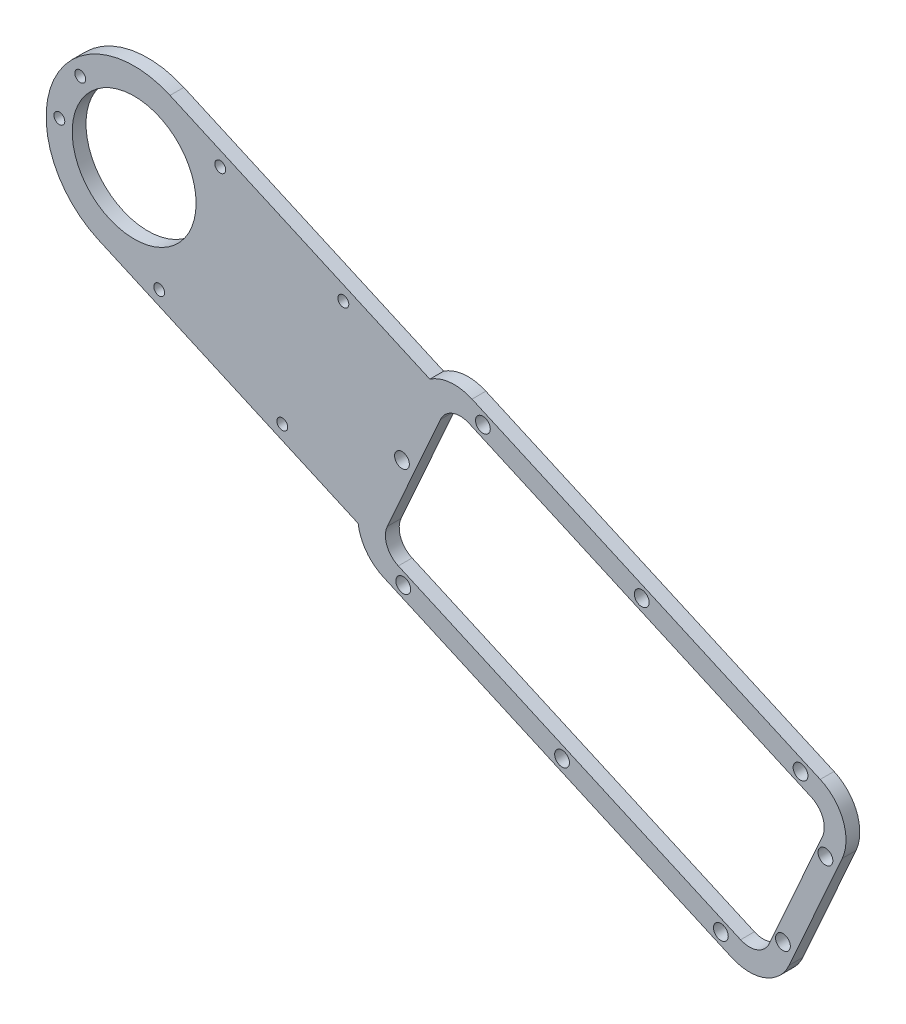
SolidWorks part; units mm, degrees
ref_plane "Front Plane" through (0, 0, 0) normal (0, 0, 1) x (1, 0, 0)
ref_plane "Top Plane" through (0, 0, 0) normal (0, 1, 0) x (1, 0, 0)
ref_plane "Right Plane" through (0, 0, 0) normal (1, 0, 0) x (0, 0, -1)
sketch "Sketch1" plane through (0, 0, 0) normal (0, 0, 1) x (1, 0, 0)
  line L0 (-81.4496, 53.8056) -> (-67.7738, 84.4844) construction
  line L1 (-91.6421, 47.2686) -> (-171.5223, 82.8771) construction
  line L2 (-75.2645, 89.2365) -> (-149.4221, 122.2941) construction
  line L3 (-72.7153, 90.8373) -> (-152.817, 126.5446)
  line L5 (-173.1746, 80.8766) -> (-93.0729, 45.1693)
  line L6 (-79.8678, 50.2314) -> (-67.6532, 77.6322)
  line L7 (-176.5357, 89.3012) -> (-161.0339, 124.0762) construction
  line L8 (-168.9326, 106.3571) -> (-73.7605, 63.9318) construction
  line L9 (-133.1238, 63.0229) -> (-112.7662, 108.691) construction
  line L10 (-162.5246, 125.6714) -> (-222.2994, 152.3174)
  line L11 (-73.7605, 63.9318) -> (-275.2251, 153.7395) construction
  line L12 (-179.0143, 88.6803) -> (-238.789, 115.3263)
  circle A0 centre (-230.5442, 133.8219) radius 14.25
  circle A2 centre (-95.5715, 49.0202) radius 1.7
  arc A3 (-152.817, 126.5446) -> (-162.5246, 125.6714) centre (-156.8885, 117.411) ccw
  arc A4 (-179.0143, 88.6803) -> (-173.1746, 80.8766) centre (-169.1031, 90.0102) ccw
  arc A5 (-93.0729, 45.1693) -> (-79.8678, 50.2314) centre (-89.0014, 54.3029) ccw
  arc A6 (-67.6532, 77.6322) -> (-72.7153, 90.8373) centre (-76.7868, 81.7037) ccw
  circle A7 centre (-132.1059, 65.3063) radius 1.7
  circle A8 centre (-168.6403, 81.5924) radius 1.7
  circle A9 centre (-150.3184, 122.6936) radius 1.7
  circle A10 centre (-113.784, 106.4076) radius 1.7
  circle A11 centre (-77.2496, 90.1215) radius 1.7
  circle A13 centre (-81.2951, 54.1522) radius 1.7
  circle A14 centre (-71.5234, 76.0729) radius 1.7
  circle A17 centre (-168.9326, 106.3571) radius 1.7
  arc A18 (-222.2994, 152.3174) -> (-238.789, 115.3263) centre (-230.5442, 133.8219) ccw
  dimension "D4" = 12
  dimension "D6" = 3.4
  dimension "D7" = 3.4
  dimension "D8" = 3.4
  dimension "D9" = 3.4
  dimension "D10" = 3.4
  dimension "D11" = 3.4
  dimension "D12" = 3.4
  dimension "D14" = 3.4
  dimension "D23" = 28.5
  dimension "D25" = 6
  dimension "D3" = 12
  dimension "D5" = 171.6559
  dimension "D1" = 2.5
  dimension "D2" = 2.5
  dimension "D15" = 0
  dimension "D16" = 0
  dimension "D17" = 40
  dimension "D18" = 40
  dimension "D20" = 40
  dimension "D21" = 40
extrude "Boss-Extrude1" add sketch "Sketch1" along normal blind 3.175
sketch "Sketch5" plane through (0, 0, 3.175) normal (0, 0, 1) x (1, 0, 0)
  line L0 (-181.3663, 93.0133) -> (-237.5676, 118.0664) construction
  line L1 (-238.789, 115.3263) -> (-179.0143, 88.6803) construction
  line L2 (-165.0202, 123.4993) -> (-223.5208, 149.5773) construction
  line L3 (-162.5246, 125.6714) -> (-222.2994, 152.3174) construction
  line L4 (-168.9326, 106.3571) -> (-249.0397, 142.0667) construction
  line L5 (-230.5442, 133.8219) -> (-247.7516, 135.033) construction
  line L6 (-242.9474, 145.8104) -> (-230.5442, 133.8219) construction
  line L7 (-196.4664, 99.7446) -> (-182.4196, 131.2555) construction
  line L8 (-224.7805, 112.3663) -> (-210.7338, 143.8772) construction
  circle A0 centre (-230.5442, 133.8219) radius 17.25 construction
  arc A1 (-222.2994, 152.3174) -> (-238.789, 115.3263) centre (-230.5442, 133.8219) ccw construction
  circle A2 centre (-196.4664, 99.7446) radius 1.25
  circle A3 centre (-224.7805, 112.3663) radius 1.25
  circle A4 centre (-210.7338, 143.8772) radius 1.25
  circle A5 centre (-182.4196, 131.2555) radius 1.25
  circle A6 centre (-242.9474, 145.8104) radius 1.25
  circle A7 centre (-247.7516, 135.033) radius 1.25
  circle A8 centre (-230.5442, 133.8219) radius 14.25 construction
  dimension "D1" = 3
  dimension "D4" = 2.5
  dimension "D5" = 2.5
  dimension "D6" = 2.5
  dimension "D7" = 2.5
  dimension "D8" = 20
  dimension "D9" = 2.5
  dimension "D10" = 20
  dimension "D11" = 2.5
  dimension "D12" = 14
  dimension "D2" = 3
  dimension "D3" = 3
  dimension "D13" = 45
extrude "Cut-Extrude4" cut sketch "Sketch5" against normal through all
sketch "Sketch6" plane through (0, 0, 3.175) normal (0, 0, 1) x (1, 0, 0)
  line L0 (-158.0596, 123.4073) -> (-70.1843, 84.2348)
  line L1 (-70.1843, 84.2348) -> (-86.4703, 47.7004)
  line L2 (-86.4703, 47.7004) -> (-174.3457, 86.8729)
  line L3 (-174.3457, 86.8729) -> (-158.0596, 123.4073)
  line L4 (-72.7153, 90.8373) -> (-152.817, 126.5446) construction
  line L5 (-173.1746, 80.8766) -> (-93.0729, 45.1693) construction
  line L6 (-79.8678, 50.2314) -> (-67.6532, 77.6322) construction
  dimension "D1" = 5
  dimension "D2" = 5
  dimension "D3" = 5
  dimension "D4" = 5
extrude "Cut-Extrude5" cut sketch "Sketch6" against normal blind 10
fillet "Fillet1" radius 5 2 edges at (-174.3457, 86.8729, 1.5875) (-158.0596, 123.4073, 1.5875)
fillet "Fillet2" radius 5 2 edges at (-86.4703, 47.7004, 1.5875) (-70.1843, 84.2348, 1.5875)
